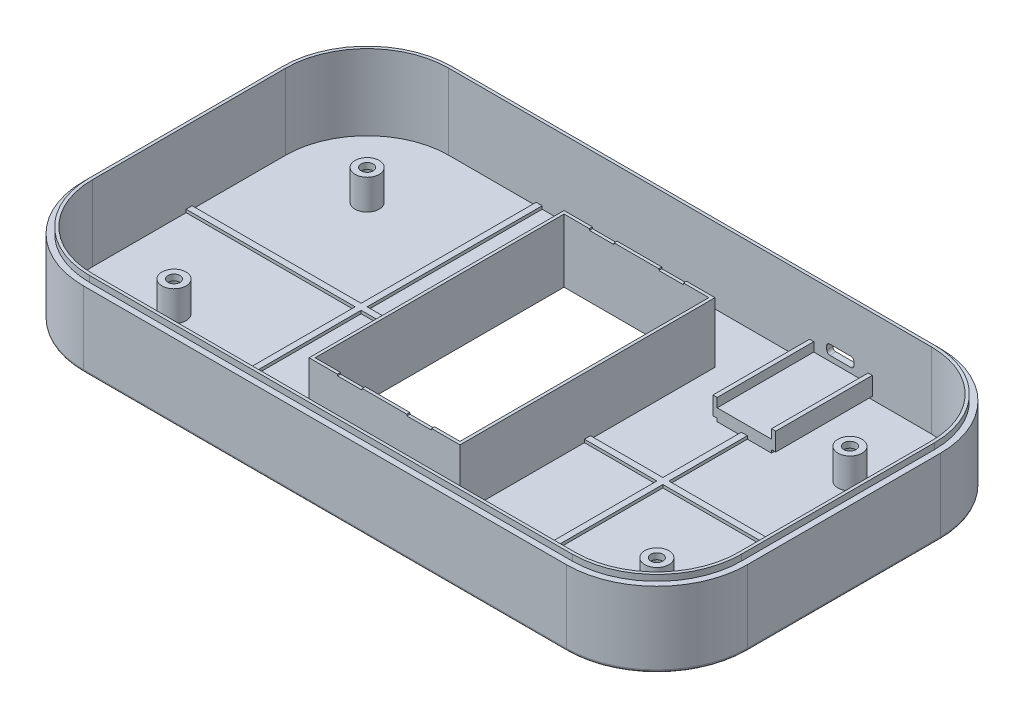
SolidWorks part; units mm, degrees
ref_plane "Front Plane" through (0, 0, 0) normal (0, 0, 1) x (1, 0, 0)
ref_plane "Top Plane" through (0, 0, 0) normal (0, 1, 0) x (1, 0, 0)
ref_plane "Right Plane" through (0, 0, 0) normal (1, 0, 0) x (0, 0, -1)
sketch "Sketch1" plane through (0, 0, 0) normal (0, 1, 0) x (1, 0, 0)
  line L1 (-80, 62) -> (80, 62)
  line L2 (-110, 32) -> (-110, -32)
  line L3 (-80, -62) -> (80, -62)
  line L4 (110, 32) -> (110, -32)
  line L5 (-110, 62) -> (110, -62) construction
  line L6 (-110, -62) -> (110, 62) construction
  arc A0 (-110, -32) -> (-80, -62) centre (-80, -32) ccw
  arc A1 (80, -62) -> (110, -32) centre (80, -32) ccw
  arc A2 (80, 62) -> (110, 32) centre (80, 32) cw
  arc A3 (-80, 62) -> (-110, 32) centre (-80, 32) ccw
  point P0 (0, 0)
  dimension "D3" = 30
  dimension "D1" = 220
  dimension "D2" = 124
extrude "Boss-Extrude1" add sketch "Sketch1" along normal blind 25
sketch "Sketch2" plane through (0, 25, 0) normal (0, 1, 0) x (1, 0, 0)
  line L8 (-80, -60) -> (80, -60)
  line L9 (108, -32) -> (108, 32)
  line L10 (80, 60) -> (-80, 60)
  line L11 (-108, 32) -> (-108, -32)
  line L12 (-80, -60) -> (80, -60)
  line L13 (108, -32) -> (108, 32)
  line L14 (80, 60) -> (-80, 60)
  line L15 (-108, 32) -> (-108, -32)
  arc A8 (-108, -32) -> (-80, -60) centre (-80, -32) ccw
  arc A9 (80, -60) -> (108, -32) centre (80, -32) ccw
  arc A10 (108, 32) -> (80, 60) centre (80, 32) ccw
  arc A11 (-80, 60) -> (-108, 32) centre (-80, 32) ccw
  arc A12 (-108, -32) -> (-80, -60) centre (-80, -32) ccw
  arc A13 (80, -60) -> (108, -32) centre (80, -32) ccw
  arc A14 (108, 32) -> (80, 60) centre (80, 32) ccw
  arc A15 (-80, 60) -> (-108, 32) centre (-80, 32) ccw
  dimension "D1" = 2
extrude "Cut-Extrude1" cut sketch "Sketch2" against normal blind 23
sketch "Sketch3" plane through (0, 2, 0) normal (0, 1, 0) x (1, 0, 0)
  line L8 (-80, -59) -> (80, -59)
  line L9 (107, -32) -> (107, 32)
  line L10 (80, 59) -> (-80, 59)
  line L11 (-107, 32) -> (-107, -32)
  line L12 (-80, -59) -> (80, -59)
  line L13 (107, -32) -> (107, 32)
  line L14 (80, 59) -> (-80, 59)
  line L15 (-107, 32) -> (-107, -32)
  line L20 (-80, -60) -> (80, -60)
  line L21 (108, -32) -> (108, 32)
  line L22 (80, 60) -> (-80, 60)
  line L23 (-108, 32) -> (-108, -32)
  line L24 (-80, -60) -> (80, -60)
  line L25 (108, -32) -> (108, 32)
  line L26 (80, 60) -> (-80, 60)
  line L27 (-108, 32) -> (-108, -32)
  arc A8 (-107, -32) -> (-80, -59) centre (-80, -32) ccw
  arc A9 (80, -59) -> (107, -32) centre (80, -32) ccw
  arc A10 (107, 32) -> (80, 59) centre (80, 32) ccw
  arc A11 (-80, 59) -> (-107, 32) centre (-80, 32) ccw
  arc A12 (-107, -32) -> (-80, -59) centre (-80, -32) ccw
  arc A13 (80, -59) -> (107, -32) centre (80, -32) ccw
  arc A14 (107, 32) -> (80, 59) centre (80, 32) ccw
  arc A15 (-80, 59) -> (-107, 32) centre (-80, 32) ccw
  arc A20 (-108, -32) -> (-80, -60) centre (-80, -32) ccw
  arc A21 (80, -60) -> (108, -32) centre (80, -32) ccw
  arc A22 (108, 32) -> (80, 60) centre (80, 32) ccw
  arc A23 (-80, 60) -> (-108, 32) centre (-80, 32) ccw
  arc A24 (-108, -32) -> (-80, -60) centre (-80, -32) ccw
  arc A25 (80, -60) -> (108, -32) centre (80, -32) ccw
  arc A26 (108, 32) -> (80, 60) centre (80, 32) ccw
  arc A27 (-80, 60) -> (-108, 32) centre (-80, 32) ccw
  dimension "D1" = 1
  dimension "D2" = 0
extrude "Boss-Extrude2" add sketch "Sketch3" along normal blind 25
sketch "Sketch5" plane through (0, 0, 0) normal (0, -1, 0) x (1, 0, 0)
  line L8 (-88, 32) -> (-88, -32)
  line L9 (-80, -40) -> (80, -40)
  line L10 (88, -32) -> (88, 32)
  line L11 (80, 40) -> (-80, 40)
  line L12 (-88, 32) -> (-88, 20)
  line L13 (-80, -40) -> (-68, -40)
  line L14 (88, -32) -> (88, -20)
  line L15 (80, 40) -> (68, 40)
  line L16 (68, -40) -> (80, -40)
  line L17 (-88, -20) -> (-88, -32)
  line L18 (68, 42) -> (68, 40)
  line L19 (90, 20) -> (88, 20)
  line L20 (-90, 32) -> (-90, -32)
  line L21 (-80, -42) -> (80, -42)
  line L22 (90, -32) -> (90, 32)
  line L23 (80, 42) -> (-80, 42)
  line L24 (-90, 32) -> (-90, 20)
  line L25 (-80, -42) -> (-68, -42)
  line L26 (90, -32) -> (90, -20)
  line L27 (80, 42) -> (68, 42)
  line L28 (90, -20) -> (88, -20)
  line L29 (68, -40) -> (68, -42)
  line L30 (-68, 42) -> (-68, 40)
  line L31 (-90, 20) -> (-88, 20)
  line L32 (-68, -40) -> (-68, -42)
  line L33 (-90, -20) -> (-88, -20)
  line L34 (-68, 42) -> (-80, 42)
  line L35 (-68, 40) -> (-80, 40)
  line L36 (68, -42) -> (80, -42)
  line L37 (90, 20) -> (90, 32)
  line L38 (88, 20) -> (88, 32)
  line L39 (-90, -20) -> (-90, -32)
  arc A8 (-80, 40) -> (-88, 32) centre (-80, 32) ccw
  arc A9 (-88, -32) -> (-80, -40) centre (-80, -32) ccw
  arc A10 (80, -40) -> (88, -32) centre (80, -32) ccw
  arc A11 (88, 32) -> (80, 40) centre (80, 32) ccw
  arc A12 (-80, 40) -> (-88, 32) centre (-80, 32) ccw
  arc A13 (-88, -32) -> (-80, -40) centre (-80, -32) ccw
  arc A14 (80, -40) -> (88, -32) centre (80, -32) ccw
  arc A15 (88, 32) -> (80, 40) centre (80, 32) ccw
  arc A20 (-80, 42) -> (-90, 32) centre (-80, 32) ccw
  arc A21 (-90, -32) -> (-80, -42) centre (-80, -32) ccw
  arc A22 (80, -42) -> (90, -32) centre (80, -32) ccw
  arc A23 (90, 32) -> (80, 42) centre (80, 32) ccw
  arc A24 (-80, 42) -> (-90, 32) centre (-80, 32) ccw
  arc A25 (-90, -32) -> (-80, -42) centre (-80, -32) ccw
  arc A26 (80, -42) -> (90, -32) centre (80, -32) ccw
  arc A27 (90, 32) -> (80, 42) centre (80, 32) ccw
  point P35 (68, 0)
  dimension "D3" = 20
  dimension "D1" = 22
  dimension "D2" = 20
extrude "Boss-Extrude3" add sketch "Sketch5" along normal blind 2
sketch "Sketch6" plane through (0, 2, 0) normal (0, 1, 0) x (1, 0, 0)
  circle A1 centre (80, 32) radius 4
  circle A2 centre (80, -32) radius 4
  circle A3 centre (-80, -32) radius 4
  circle A4 centre (-80, 32) radius 4
  dimension "D1" = 8
extrude "Boss-Extrude4" add sketch "Sketch6" along normal blind 10
sketch "Sketch7" plane through (0, 12, 0) normal (0, 1, 0) x (1, 0, 0)
  line L0 (107, 0) -> (81.6257, 0)
  line L1 (107, -32) -> (107, 32) construction
  line L2 (0, 7.0485) -> (0, 59)
  line L3 (80, 59) -> (-80, 59) construction
  circle A0 centre (80, 32) radius 2
  circle A1 centre (80, -32) radius 2
  circle A2 centre (-80, -32) radius 2
  circle A3 centre (-80, 32) radius 2
  dimension "D1" = 4
extrude "Cut-Extrude2" cut sketch "Sketch7" against normal blind 54 contours A3 | A2 | A0 | A1
sketch "Sketch8" plane through (0, 0, 0) normal (0, -1, 0) x (1, 0, 0)
  circle A0 centre (-80, 32) radius 3.5
  circle A1 centre (-80, -32) radius 3.5
  circle A2 centre (80, -32) radius 3.5
  circle A3 centre (80, 32) radius 3.5
  dimension "D1" = 7
extrude "Cut-Extrude3" cut sketch "Sketch8" against normal blind 10
sketch "Sketch9" plane through (0, 2, 0) normal (0, 1, 0) x (1, 0, 0)
  line L0 (49, -59) -> (51, -59)
  line L4 (49, -1) -> (49, -59)
  line L6 (-1, -59) -> (1, -59)
  line L9 (-49, 59) -> (-51, 59)
  line L10 (-49, -1) -> (-49, -59)
  line L13 (1, 59) -> (-1, 59)
  line L14 (-1, 1) -> (-49, 1)
  line L15 (-51, 59) -> (-51, 1)
  line L16 (-80, -59) -> (80, -59)
  line L17 (107, -32) -> (107, 32)
  line L18 (80, 59) -> (-80, 59)
  line L19 (-107, 32) -> (-107, -32)
  line L20 (-51, -59) -> (-49, -59)
  line L21 (107, -1) -> (107, 1)
  line L22 (51, 59) -> (49, 59)
  line L23 (-107, 1) -> (-107, -1)
  line L24 (-1, 59) -> (-1, 1)
  line L25 (-1, -1) -> (-1, -59)
  line L26 (49, 59) -> (49, 1)
  line L27 (1, -1) -> (49, -1)
  line L28 (-1, -1) -> (-49, -1)
  line L29 (-49, 59) -> (-49, 1)
  line L30 (1, 59) -> (1, 1)
  line L31 (1, -1) -> (1, -59)
  line L32 (51, 59) -> (51, 1)
  line L33 (1, 1) -> (49, 1)
  line L34 (-51, -1) -> (-107, -1)
  line L38 (51, -1) -> (51, -59)
  line L39 (-51, -1) -> (-51, -59)
  line L41 (-51, 1) -> (-107, 1)
  line L42 (51, -1) -> (107, -1)
  line L44 (51, 1) -> (107, 1)
  arc A8 (-107, -32) -> (-80, -59) centre (-80, -32) ccw
  arc A9 (80, -59) -> (107, -32) centre (80, -32) ccw
  arc A10 (107, 32) -> (80, 59) centre (80, 32) ccw
  arc A11 (-80, 59) -> (-107, 32) centre (-80, 32) ccw
  dimension "D1" = 0
extrude "Boss-Extrude5" add sketch "Sketch9" along normal blind 1
fillet "Fillet1" radius 1 8 edges at (-101.2132, 0, -53.2132) (0, 0, -62) (101.2132, 0, -53.2132) (110, 0, 0) (101.2132, 0, 53.2132) (0, 0, 62) (-101.2132, 0, 53.2132) (-110, 0, 0)
sketch "Sketch11" plane through (0, 0, 0) normal (0, -1, 0) x (1, 0, 0)
  line L0 (0, 61) -> (0, -61)
  line L1 (80, 61) -> (-80, 61) construction
  line L2 (-80, -61) -> (80, -61) construction
  line L4 (-25, 42.25) -> (25, 42.25)
  line L5 (-25, 42.25) -> (-25, -42.25)
  line L6 (-25, -42.25) -> (25, -42.25)
  line L7 (25, 42.25) -> (25, -42.25)
  line L8 (-25, 42.25) -> (25, -42.25) construction
  line L9 (-25, -42.25) -> (25, 42.25) construction
  point P6 (0, 0)
  dimension "D1" = 84.5
  dimension "D2" = 50
extrude "Boss-Extrude7" add sketch "Sketch11" against normal blind 22 contours L7 L4 L0 L6 | L5 L6 L0 L4
sketch "Sketch12" plane through (0, 22, 0) normal (0, 1, 0) x (1, 0, 0)
  line L0 (-25, 42.25) -> (25, -42.25)
  line L2 (24, 41.25) -> (-24, 41.25)
  line L3 (24, 41.25) -> (24, -41.25)
  line L4 (24, -41.25) -> (-24, -41.25)
  line L5 (-24, 41.25) -> (-24, -41.25)
  line L6 (24, 41.25) -> (-24, -41.25) construction
  line L7 (24, -41.25) -> (-24, 41.25) construction
  point P4 (0, 0)
  dimension "D1" = 48
  dimension "D2" = 82.5
extrude "Cut-Extrude4" cut sketch "Sketch12" against normal blind 34.5484 contours L2 L5 L0 L3 | L0 L5 L4 L3
sketch "Sketch13" plane through (0, 0, 42.25) normal (0, 0, 1) x (1, 0, 0)
  line L0 (-15.6, 22.0009) -> (-7.4, 22.0009)
  line L1 (0, 21) -> (0, 0)
  line L2 (-15.6, 22.0009) -> (-15.6, 21.5009)
  line L3 (-25, 22) -> (-25, 2) construction
  line L4 (-15.6, 21.5009) -> (-7.4, 21.5009)
  line L5 (-7.4, 21.5009) -> (-7.4, 22.0009)
  line L6 (7.4, 22.0009) -> (15.6, 22.0009)
  line L7 (7.4, 21.5009) -> (7.4, 22.0009)
  line L8 (15.6, 21.5009) -> (7.4, 21.5009)
  line L9 (15.6, 22.0009) -> (15.6, 21.5009)
  line M7 (25, 22) -> (-25, 22)
  dimension "D1" = 9.4
  dimension "D2" = 8.2
  dimension "D3" = 0.5
extrude "Cut-Extrude5" cut sketch "Sketch13" against normal blind 94.5484 contours L9 L7 L8 M7 | L4 L5 L2 M7
sketch "Sketch14" plane through (0, 0, 0) normal (0, -1, 0) x (1, 0, 0)
  line L0 (24, 41.25) -> (24, -41.25)
  line L4 (-27, 44) -> (27, 44)
  line L5 (-27, 44) -> (-27, -44)
  line L6 (-27, -44) -> (27, -44)
  line L7 (27, 44) -> (27, -44)
  line L10 (-24, 41.25) -> (24, 41.25)
  line L11 (-24, 41.25) -> (-24, -41.25)
  point P6 (0, 0)
  point P12 (0, 0)
  line M1 (24, 41.25) -> (24, -41.25)
  line M2 (24, -41.25) -> (-24, -41.25)
  line M3 (-24, -41.25) -> (-24, 41.25)
  line M4 (-24, 41.25) -> (24, 41.25)
  dimension "D1" = 88
  dimension "D2" = 54
extrude "Cut-Extrude6" cut sketch "Sketch14" against normal blind 1 contours L7 L4 L5 L6 M4 M1 M2 M3
sketch "Sketch15" plane through (0, 1, 0) normal (0, -1, 0) x (1, 0, 0)
  line L0 (0, -42.625) -> (0, -41.25)
  line L1 (-27, -44) -> (27, -44) construction
  line L2 (24, -41.25) -> (-24, -41.25) construction
  line L3 (-4, -44) -> (4, -44)
  line L4 (4, -44) -> (4, -42.6558)
  line L5 (4, -42.6558) -> (0, -42.625)
  line L6 (-4, -44) -> (-4, -42.6558)
  line L7 (-4, -42.6558) -> (0, -42.625)
  line M4 (-27, -44) -> (27, -44)
  dimension "D1" = 4
extrude "Cut-Extrude7" cut sketch "Sketch15" against normal blind 2 contours L7 L6 L4 L5 M4
sketch "Sketch16" plane through (0, 3, 0) normal (0, 1, 0) x (1, 0, 0)
  line L3 (-4, 50) -> (4, 50)
  line L4 (-4, 50) -> (-4, 44)
  line L5 (-4, 44) -> (4, 44)
  line L6 (4, 50) -> (4, 44)
  dimension "D1" = 6
extrude "Cut-Extrude9" cut sketch "Sketch16" against normal blind 2
sketch "Sketch17" plane through (0, 2, 0) normal (0, 1, 0) x (1, 0, 0)
  line L2 (59, 59) -> (41, 59)
  line L3 (49, 59) -> (1, 59) construction
  line L4 (41, 59) -> (41, 27)
  line L5 (41, 27) -> (59, 27)
  line L6 (59, 59) -> (59, 27)
  dimension "D1" = 18
  dimension "D2" = 18
  dimension "D3" = 32
extrude "Boss-Extrude8" add sketch "Sketch17" along normal blind 4
sketch "Sketch18" plane through (0, 6, 0) normal (0, 1, 0) x (1, 0, 0)
  line L1 (41, 59) -> (41, 27)
  line L2 (39.6097, 59) -> (41, 59)
  line L3 (39.6097, 59) -> (39.6097, 27)
  line L4 (39.6097, 27) -> (41, 27)
  line L5 (60.3903, 59) -> (60.3903, 27)
  line L8 (59, 59) -> (59, 27)
  line L9 (59, 27) -> (60.3903, 27)
  line L12 (59, 59) -> (60.3903, 59)
  point P4 (50, 43)
extrude "Boss-Extrude9" add sketch "Sketch18" along normal mid plane 6
sketch "Sketch19" plane through (0, 0, -59) normal (0, 0, 1) x (1, 0, 0)
  line L0 (45.3, 7.75) -> (54.3, 7.75)
  line L1 (59, 6) -> (41, 6) construction
  line L4 (54.3, 7.75) -> (54.3, 10.95)
  line L5 (54.3, 10.95) -> (45.3, 10.95)
  line L6 (45.3, 7.75) -> (45.3, 10.95)
  point P10 (49.8, 10.95)
  dimension "D1" = 3.2
  dimension "D2" = 1.75
  dimension "D3" = 4.5
extrude "Cut-Extrude10" cut sketch "Sketch19" against normal blind 6
fillet "Fillet2" radius 1 1 edges at (54.3, 7.75, -60.5)
fillet "Fillet3" radius 1 1 edges at (45.3, 7.75, -60.5)
fillet "Fillet4" radius 1 1 edges at (45.3, 10.95, -60.5)
fillet "Fillet5" radius 1 1 edges at (54.3, 10.95, -60.5)
sketch "Sketch20" plane through (0, 0, -62) normal (0, 0, -1) x (-1, 0, 0)
  line L4 (-56.2498, 12.4084) -> (-43.3502, 12.4084)
  line L5 (-57.7498, 10.9084) -> (-57.7498, 7.7916)
  line L6 (-56.2498, 6.2916) -> (-43.3502, 6.2916)
  line L7 (-41.8502, 10.9084) -> (-41.8502, 7.7916)
  arc A0 (-43.3502, 6.2916) -> (-41.8502, 7.7916) centre (-43.3502, 7.7916) ccw
  arc A1 (-57.7498, 7.7916) -> (-56.2498, 6.2916) centre (-56.2498, 7.7916) ccw
  arc A2 (-56.2498, 12.4084) -> (-57.7498, 10.9084) centre (-56.2498, 10.9084) ccw
  arc A3 (-43.3502, 12.4084) -> (-41.8502, 10.9084) centre (-43.3502, 10.9084) cw
  point P6 (-49.8, 9.35)
  dimension "D1" = 1.5
extrude "Cut-Extrude12" cut sketch "Sketch20" against normal blind 1
